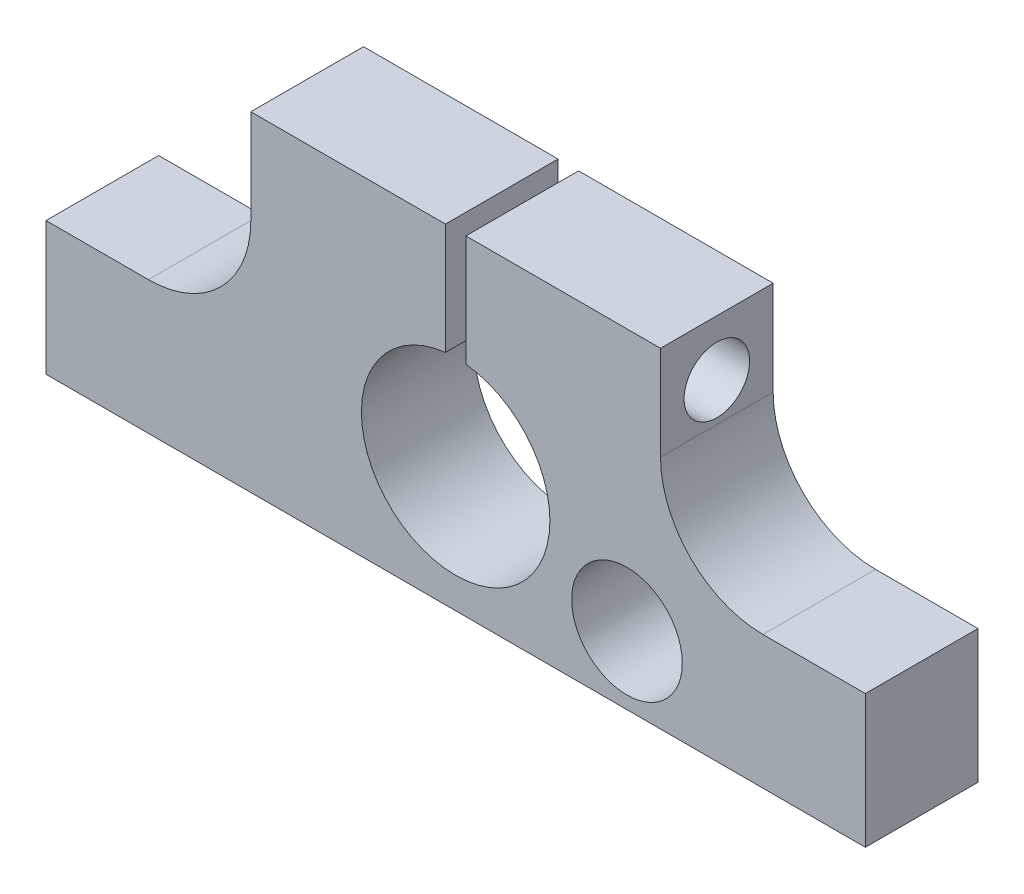
SolidWorks part; units mm, degrees
ref_plane "Płaszczyzna przednia" through (0, 0, 0) normal (0, 0, 1) x (1, 0, 0)
ref_plane "Płaszczyzna górna" through (0, 0, 0) normal (0, 1, 0) x (1, 0, 0)
ref_plane "Płaszczyzna prawa" through (0, 0, 0) normal (1, 0, 0) x (0, 0, -1)
sketch "Szkic1" plane through (0, 0, 0) normal (0, 0, 1) x (1, 0, 0)
  line L1 (-10, 6.1) -> (10, 6.1)
  line L2 (-10, 6.1) -> (-10, -10)
  line L3 (-10, -10) -> (10, -10)
  line L4 (10, 6.1) -> (10, -10)
  line L7 (-20, -10) -> (20, -10)
  line L8 (-20, -10) -> (-20, -3.5)
  line L9 (-20, -3.5) -> (20, -3.5)
  line L10 (20, -10) -> (20, -3.5)
  circle A0 centre (0, -3.9) radius 4.6008
  dimension "D1" = 20
  dimension "D2" = 10
  dimension "D3" = 40
  dimension "D4" = 10
  dimension "D5" = 6.5
  dimension "D6" = 6.1
extrude "Dodanie-wyciągnięcie1" add sketch "Szkic1" along normal blind 5.5 contours A0 L9 L4 L1 L2 | L9 L8 L7 L2 | A0 L9 L2 L3 L4 | L7 L10 L9 L4
sketch "Szkic2" plane through (0, 6.1, 0) normal (0, 1, 0) x (1, 0, 0)
  line L0 (0, 0) -> (0, -5.5) construction
  line L1 (-10, -5.5) -> (10, -5.5) construction
  line L3 (-0.5, 0) -> (0.5, 0)
  line L4 (-0.5, 0) -> (-0.5, -5.5)
  line L5 (-0.5, -5.5) -> (0.5, -5.5)
  line L6 (0.5, 0) -> (0.5, -5.5)
  line L7 (-0.5, 0) -> (0.5, -5.5) construction
  line L8 (-0.5, -5.5) -> (0.5, 0) construction
  point P5 (0, -2.75)
  dimension "D1" = 1
extrude "Wytnij-wyciągnięcie1" cut sketch "Szkic2" against normal up to next contours L4 L3 L6 L5
sketch "Szkic3" plane through (10, 0, 0) normal (1, 0, 0) x (0, 0, -1)
  line L0 (0, 0.6736) -> (-5.5, 0.6736) construction
  line L1 (0, 0.6736) -> (-5.5, 0.6736)
  line L2 (-2.75, 6.1) -> (-2.75, 0.6736) construction
  line L3 (-5.5, 6.1) -> (0, 6.1) construction
  point P6 (-2.75, 3.3868)
hole_wizard "Otwór gwintowany M3x0.51" positions "Szkic4" profile "Szkic6" tap size "M3x0.5" standard "Ansi Metric"
sketch "Szkic4" plane through (10, 0, 0) normal (1, 0, 0) x (0, 0, -1)
  point P0 (-2.75, 3.3868)
sketch "Szkic6" plane through (10, 3.3868, 2.75) normal (0, 1, 0) x (0, 0, -1)
  line L0 (0, 0) -> (0, 20.7501)
  line L1 (0, 20.7501) -> (1.25, 19.999)
  line L2 (1.25, 19.999) -> (1.25, 0)
  line L5 (1.25, 0) -> (0, 0)
  line L10 (0, 20.7501) -> (-1.25, 19.999) construction
  line L11 (0, -6.35) -> (0, 107.95) construction
  dimension "Średnica wiertła gwintu" = 2.5
  dimension "Głębokość otworu gwintowanego" = 19.999
  dimension "Kąt wiertła" = 118
cosmetic thread "Gwint otworu1" parameters "D1"=6, "D2"=3
hole_wizard "Otwór pod śrubę M31" positions "Szkic7" profile "Szkic9" hole size "M3" standard "Ansi Metric"
sketch "Szkic7" plane through (10, 0, 0) normal (1, 0, 0) x (0, 0, -1)
  point P0 (-2.75, 3.3868)
sketch "Szkic9" plane through (10, 3.3868, 2.75) normal (0, 1, 0) x (0, 0, -1)
  line L0 (0, 0) -> (0, 10.4604)
  line L1 (0, 10.4604) -> (1.6, 9.499)
  line L2 (1.6, 9.499) -> (1.6, 0)
  line L5 (1.6, 0) -> (0, 0)
  line L10 (0, 10.4604) -> (-1.6, 9.499) construction
  line L11 (0, -6.35) -> (0, 107.95) construction
  dimension "Średnica otworu" = 3.2
  dimension "Głębokość otworu" = 9.499
  dimension "Kąt wiertła" = 118
sketch "Szkic10" plane through (0, 0, 5.5) normal (0, 0, 1) x (1, 0, 0)
  circle A0 centre (8.3631, -6.6796) radius 2.7
  point P2 (7.2953, -6.3865)
  point P3 (8.3631, -6.6796)
extrude "Wytnij-wyciągnięcie2" cut sketch "Szkic10" against normal through all
fillet "Zaokrąglenie1" radius 5 2 edges at (-10, -3.5, 2.75) (10, -3.5, 2.75)
